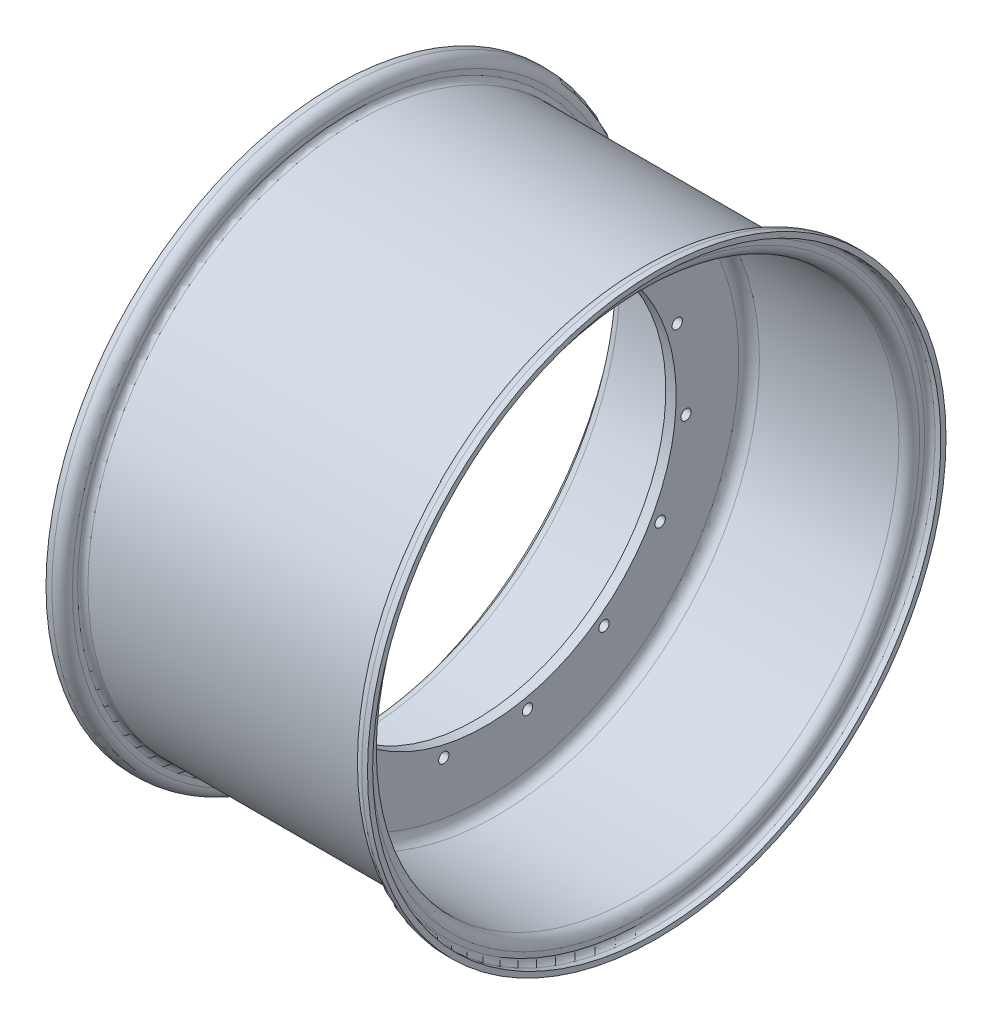
SolidWorks part; units mm, degrees
material "7075-T6 (SN)"
ref_plane "Front Plane" through (0, 0, 0) normal (0, 0, 1) x (1, 0, 0)
ref_plane "Top Plane" through (0, 0, 0) normal (0, 1, 0) x (1, 0, 0)
ref_plane "Right Plane" through (0, 0, 0) normal (1, 0, 0) x (0, 0, -1)
sketch "Sketch1" plane through (0, 0, 0) normal (0, 0, 1) x (1, 0, 0)
  line L0 (0, 0) -> (0, 165.1) construction
  line L1 (0, 165.1) -> (95.25, 165.1)
  line L2 (98.425, 168.275) -> (98.425, 171.45)
  line L3 (104.775, 177.8) -> (108.331, 177.8)
  line L4 (0, 165.1) -> (-76.2, 165.1)
  line L5 (-79.375, 168.275) -> (-79.375, 171.45)
  line L6 (-85.725, 177.8) -> (-89.281, 177.8)
  line L7 (104.775, 174.625) -> (108.331, 174.625)
  line L8 (101.6, 168.275) -> (101.6, 171.45)
  line L9 (3.175, 161.925) -> (95.25, 161.925)
  line L10 (-76.2, 161.925) -> (-3.175, 161.925)
  line L11 (-82.55, 168.275) -> (-82.55, 171.45)
  line L12 (-89.281, 174.625) -> (-85.725, 174.625)
  line L13 (108.331, 174.625) -> (108.331, 177.8)
  line L14 (-89.281, 177.8) -> (-89.281, 174.625)
  line L15 (-3.175, 0) -> (-3.175, 161.925) construction
  line L16 (-87.0379, 0) -> (87.0379, 0) construction
  line L17 (-3.175, 161.925) -> (-3.175, 117.094)
  line L18 (-3.175, 117.094) -> (3.175, 117.094)
  line L19 (3.175, 117.094) -> (3.175, 161.925)
  line L20 (0, 161.925) -> (-76.2, 161.925) construction
  line L21 (0, 161.925) -> (95.25, 161.925) construction
  line L22 (-82.55, 168.275) -> (-82.55, 171.45) construction
  line L23 (-85.725, 174.625) -> (-89.281, 174.625) construction
  arc A0 (101.6, 171.45) -> (104.775, 174.625) centre (104.775, 171.45) cw
  arc A1 (95.25, 165.1) -> (98.425, 168.275) centre (95.25, 168.275) ccw
  arc A2 (98.425, 171.45) -> (104.775, 177.8) centre (104.775, 171.45) cw
  arc A3 (95.25, 161.925) -> (101.6, 168.275) centre (95.25, 168.275) ccw
  arc A4 (-76.2, 165.1) -> (-79.375, 168.275) centre (-76.2, 168.275) cw
  arc A5 (-79.375, 171.45) -> (-85.725, 177.8) centre (-85.725, 171.45) ccw
  arc A6 (-76.2, 161.925) -> (-82.55, 168.275) centre (-76.2, 168.275) cw
  arc A7 (-82.55, 171.45) -> (-85.725, 174.625) centre (-85.725, 171.45) ccw
  arc A8 (-82.55, 171.45) -> (-85.725, 174.625) centre (-85.725, 171.45) ccw construction
  arc A11 (-76.2, 161.925) -> (-82.55, 168.275) centre (-76.2, 168.275) cw construction
  dimension "D1" = 3.175
  dimension "D3" = 3.175
  dimension "D12" = 6.35
  dimension "D13" = 6.35
  dimension "D2" = 177.8
  dimension "D4" = 9.906
  dimension "D5" = 9.906
  dimension "D6" = 12.7
  dimension "D7" = 3.175
  dimension "D8" = 6.35
  dimension "D9" = 76.2
  dimension "D10" = 117.094
  dimension "D11" = 330.2
  dimension "D15" = 3.175
revolve "Revolve1" add sketch "Sketch1" angle 360 about L16
sketch3d "3DSketch1" [suppressed]
  line L0 (-26.416, 0, 0) -> (-29.972, 0, 0) construction
  line L1 (167.64, 0, 0) -> (164.084, 0, 0) construction
  line L2 (167.64, 0, 0) -> (164.084, 0, 0) construction
  line L3 (142.24, 0, 0) -> (-29.972, 0, 0) construction
  line L4 (-23.241, 0, 0) -> (-29.972, 0, 0) construction
  line L5 (142.24, 0, 0) -> (142.24, -170.1747, 0) construction
  line L6 (-29.972, 0, 0) -> (-29.972, -170.1747, 0) construction
  line L7 (-29.972, -170.1747, 0) -> (142.24, -170.1747, 0) construction
  circle A1 centre (142.24, 0, 0) radius 170.1747 construction
  circle A2 centre (-29.972, 0, 0) radius 170.1747 construction
  point P0 (-29.972, 0, 0)
  point P1 (142.24, 0, 0)
  point P10 (-27.9347, 0, 0)
  point P15 (56.134, 0, 0)
  point P20 (-200.1467, 0, 0)
  point P21 (56.134, -170.1747, 0)
sketch "Sketch2" plane through (-3.175, 0, 0) normal (-1, 0, 0) x (0, 0, 1)
  line L0 (0, 0) -> (0, 123.825) construction
  circle A0 centre (0, 123.825) radius 3.175
  dimension "D1" = 6.35
  dimension "D2" = 123.825
extrude "Cut-Extrude1" cut sketch "Sketch2" against normal through all
pattern_circular "CirPattern1" count 15 over 360 about axis through (0, 0, 0) along (1, 0, 0) of "Cut-Extrude1"
fillet "Fillet1" radius 6.35 2 edges at (-3.175, 0, 161.925) (3.175, 0, 161.925)
ref_plane "Mid Plane" [suppressed] through (60.325, 0, 0) normal (1, 0, 0) x (0, 0, -1)
